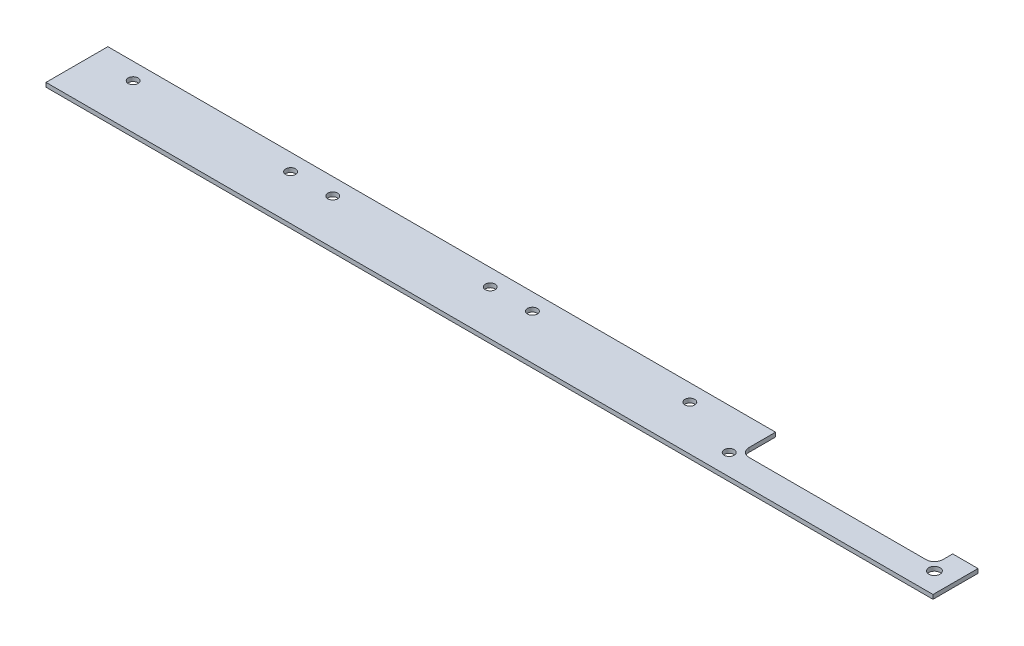
SolidWorks part; units mm, degrees
material "Простая углеродистая сталь"
ref_plane "Спереди" through (0, 0, 0) normal (0, 0, 1) x (1, 0, 0)
ref_plane "Сверху" through (0, 0, 0) normal (0, 1, 0) x (1, 0, 0)
ref_plane "Справа" through (0, 0, 0) normal (1, 0, 0) x (0, 0, -1)
sketch "Эскиз1" plane through (0, 0, 0) normal (0, 1, 0) x (1, 0, 0)
  line L0 (237.5, 22) -> (237.5, 12.5)
  line L1 (0, 0) -> (315.5, 0)
  line L2 (0, 0) -> (0, 22)
  line L3 (0, 22) -> (237.5, 22)
  line L5 (240.5, 9.5) -> (303.5, 9.5)
  line L7 (306.5, 12.5) -> (306.5, 16)
  line L8 (306.5, 16) -> (315.5, 16)
  line L9 (315.5, 16) -> (315.5, 0)
  circle A1 centre (235.5, 7.5) radius 1.75
  circle A2 centre (71, 16) radius 1.75
  circle A3 centre (15, 16) radius 1.75
  circle A4 centre (86, 16) radius 1.75
  circle A5 centre (142, 16) radius 1.75
  circle A8 centre (308.5, 7.5) radius 2
  arc A9 (237.5, 12.5) -> (240.5, 9.5) centre (240.5, 12.5) ccw
  arc A10 (303.5, 9.5) -> (306.5, 12.5) centre (303.5, 12.5) ccw
  circle A11 centre (157, 16) radius 1.75
  circle A12 centre (213, 16) radius 1.75
  dimension "D2" = 3
  dimension "D3" = 3
  dimension "D1" = 3
extrude "Бобышка-Вытянуть1" add sketch "Эскиз1" along normal blind 1.5 contours L2 L1 L3
